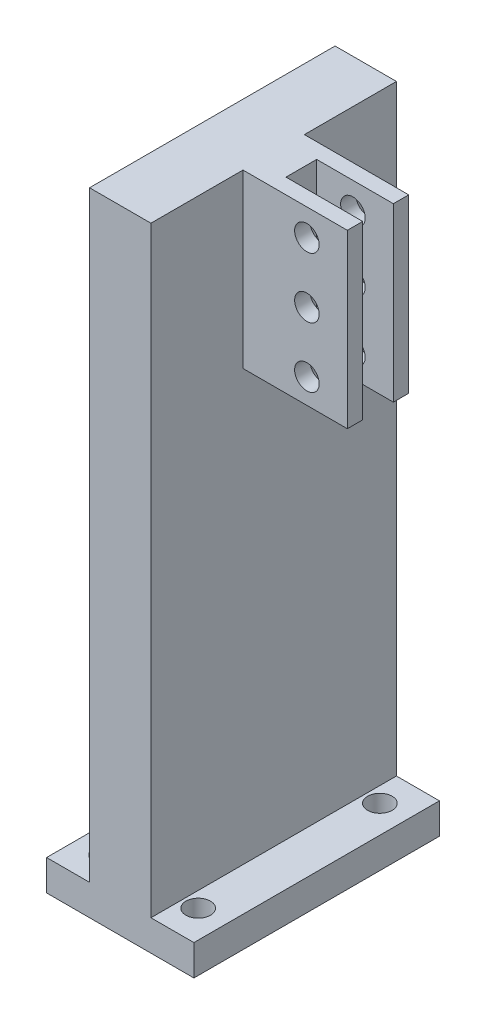
SolidWorks part; units mm, degrees
material "1060 合金"
ref_plane "Front" through (0, 0, 0) normal (0, 0, 1) x (1, 0, 0)
ref_plane "Top" through (0, 0, 0) normal (0, 1, 0) x (1, 0, 0)
ref_plane "Right" through (0, 0, 0) normal (1, 0, 0) x (0, 0, -1)
sketch "草图1" plane through (0, 0, 0) normal (0, 1, 0) x (1, 0, 0)
  line L0 (0, 0) -> (0, -14.8) construction
  line L1 (-20, 20) -> (20, 20) construction
  line L2 (20, 20) -> (20, -20) construction
  line L3 (20, 0) -> (0, 0) construction
  line L4 (0, 0) -> (0, 20) construction
  line L5 (0, 20) -> (12, 20) construction
  line L6 (-20, 20) -> (-20, -20) construction
  line L7 (-20, -20) -> (20, -20) construction
  line L12 (0, -14.8) -> (7.5, -14.8) construction
  line L13 (0, -14.8) -> (-7.5, -14.8) construction
  line L14 (12, 20) -> (12, -20) construction
  line L15 (12, -20) -> (-12, -20)
  line L16 (12, -20) -> (12, 20)
  line L17 (12, 20) -> (-12, 20)
  line L18 (-12, -20) -> (-12, 20)
  circle A4 centre (7.5, -14.8) radius 2
  circle A5 centre (-7.5, -14.8) radius 2
  circle A6 centre (-7.5, 14.8) radius 2
  circle A7 centre (7.5, 14.8) radius 2
  point P13 (10, 0)
  point P14 (-10, 0)
  point P16 (-20, 0)
  point P22 (12, 0)
  point P26 (0, -20)
extrude "凸台-拉伸1" add sketch "草图1" along normal blind 5
sketch "草图8" plane through (0, 5, 0) normal (0, 1, 0) x (1, 0, 0)
  line L0 (0, 0) -> (5, 0) construction
  line L1 (0, 0) -> (-5, 0) construction
  line L2 (-5, 0) -> (-5, -20)
  line L3 (-12, -20) -> (12, -20) construction
  line L4 (-5, -20) -> (5, -20)
  line L5 (5, -20) -> (5, 20)
  line L6 (12, 20) -> (-12, 20) construction
  line L7 (5, 20) -> (-5, 20)
  line L8 (-5, 20) -> (-5, 0)
  line L9 (5, 20) -> (12, 20) construction
extrude "凸台-拉伸5" add sketch "草图8" along normal blind 98
sketch "草图10" plane through (5, 0, 0) normal (1, 0, 0) x (0, 0, -1)
  line L0 (0, 103) -> (5, 103) construction
  line L1 (-20, 103) -> (20, 103) construction
  line L2 (5, 103) -> (5, 75) construction
  line L3 (5, 75) -> (-5, 75) construction
  line L4 (-5, 75) -> (-5, 103) construction
  line L5 (-5, 103) -> (0, 103) construction
  line L6 (-5, 103) -> (5, 103)
  line L7 (5, 103) -> (5, 75)
  line L8 (5, 75) -> (-5, 75)
  line L9 (-5, 75) -> (-5, 103)
extrude "凸台-拉伸6" add sketch "草图10" along normal blind 18.5
sketch "草图12" plane through (0, 0, -5) normal (0, 0, -1) x (-1, 0, 0)
  line L0 (-23.5, 103) -> (-11.5, 103) construction
  line L1 (-23.5, 103) -> (-5, 103) construction
  line L2 (-17.5, 98.67) -> (-17.5, 88.85) construction
  line L3 (-17.5, 98.67) -> (-21.41, 98.67) construction
  line L4 (-17.5, 88.85) -> (-21.41, 88.85) construction
  line L5 (-21.41, 88.85) -> (-21.41, 79.03) construction
  line L6 (-11.5, 103) -> (-11.5, 98.67) construction
  line L7 (-11.5, 98.67) -> (-15.41, 98.67) construction
  line L8 (-15.41, 98.67) -> (-15.41, 88.85) construction
  line L9 (-15.41, 88.85) -> (-11.5, 88.85) construction
  line L10 (-11.5, 88.85) -> (-11.5, 79.03) construction
  line L11 (-11.5, 79.03) -> (-15.41, 79.03) construction
  line L12 (-11.5, 79.03) -> (-6.9723, 79.03) construction
  line L13 (-6.9723, 79.03) -> (-6.9723, 75) construction
  line L14 (-23.5, 75) -> (-5, 75) construction
  circle A3 centre (-15.41, 98.67) radius 2
  circle A4 centre (-15.41, 88.85) radius 2
  circle A5 centre (-15.41, 79.03) radius 2
extrude "切除-拉伸4" cut sketch "草图12" against normal mid plane 48.5
sketch "草图13" plane through (0, 0, 0) normal (0, 0, 1) x (1, 0, 0)
  line L0 (23.5, 103) -> (11.5, 103)
  line L1 (23.5, 103) -> (5, 103) construction
  line L5 (23.5, 75) -> (23.5, 103)
  line L6 (11.5, 103) -> (11.5, 75)
  line L7 (23.5, 75) -> (5, 75) construction
  line L8 (11.5, 75) -> (23.5, 75)
extrude "切除-拉伸5" cut sketch "草图13" against normal mid plane 4
sketch "草图14" plane through (0, 103, 0) normal (0, 1, 0) x (1, 0, 0)
  line L0 (11.5, 0) -> (9.5, 0) construction
  line L1 (11.5, 2) -> (11.5, -2) construction
  line L2 (11.5, 2) -> (9.5, 2) construction
  line L3 (11.5, -2) -> (9.5, -2) construction
  line L4 (11.5, 2) -> (9.5, 2)
  line L5 (9.5, 2) -> (9.5, -2)
  line L6 (9.5, -2) -> (11.5, -2)
  line L7 (11.5, -2) -> (11.5, 2)
  line L8 (23.5, 5) -> (22, 5) construction
  line L9 (23.5, 5) -> (5, 5) construction
  line L10 (22, 5) -> (22, -5) construction
  line L11 (23.5, -5) -> (5, -5) construction
  line L12 (22, -5) -> (23.5, -5) construction
  line L13 (23.5, -5) -> (23.5, 5) construction
  line L14 (22, 5) -> (23.5, 5)
  line L15 (23.5, 5) -> (23.5, 2)
  line L16 (23.5, -5) -> (22, -5)
  line L17 (22, -5) -> (22, -2.5)
  line L18 (22, 2.5) -> (22, -2.5)
  line L19 (23.5, 2) -> (23.5, -2)
  line L30 (22, 2.5) -> (22, 5)
  line L32 (23.5, -2) -> (23.5, -5)
extrude "切除-拉伸6" cut sketch "草图14" against normal blind 34
sketch "草图15" plane through (0, 103, 0) normal (0, 1, 0) x (1, 0, 0)
  line L0 (9.5, 2) -> (9.5, 2.5) construction
  line L1 (9.5, 2.5) -> (22, 2.5) construction
  line L2 (22, 5) -> (22, 2) construction
  line L3 (9.5, -2) -> (9.5, -2.5) construction
  line L4 (9.5, -2.5) -> (22, -2.5) construction
  line L5 (22, -2) -> (22, -5) construction
  line L6 (9.5, 2) -> (9.5, 2.5)
  line L7 (9.5, 2.5) -> (22, 2.5)
  line L8 (22, 2.5) -> (22, 2)
  line L9 (22, 2) -> (9.5, 2)
  line L10 (9.5, -2) -> (9.5, -2.5)
  line L11 (9.5, -2.5) -> (22, -2.5)
  line L12 (22, -2.5) -> (22, -2)
  line L13 (22, -2) -> (9.5, -2)
extrude "切除-拉伸7" cut sketch "草图15" against normal blind 34
